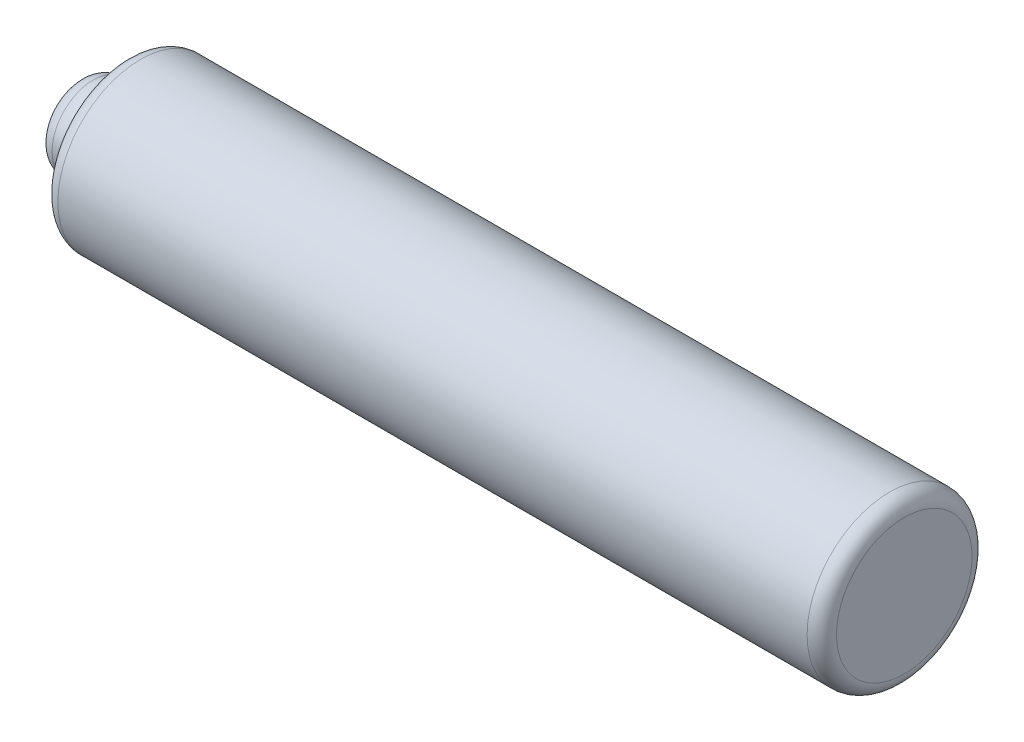
SolidWorks part; units mm, degrees
material "Copper"
ref_plane "Front Plane" through (0, 0, 0) normal (0, 0, 1) x (1, 0, 0)
ref_plane "Top Plane" through (0, 0, 0) normal (0, 1, 0) x (1, 0, 0)
ref_plane "Right Plane" through (0, 0, 0) normal (1, 0, 0) x (0, 0, -1)
sketch "Sketch1" plane through (0, 0, 0) normal (0, 1, 0) x (1, 0, 0)
  line L1 (-45.8444, 21.4949) -> (-5.4513, 21.4949)
  line L2 (-45.8444, 21.4949) -> (-45.8444, 19.355)
  line L3 (-45.8444, 17.2152) -> (-5.4513, 17.2152)
  line L4 (-5.4513, 21.4949) -> (-5.4513, 17.2152)
  line L5 (-45.8444, 19.355) -> (-48.2854, 19.355)
  line L7 (-45.8444, 17.2152) -> (-48.2854, 17.2152)
  line L8 (-48.2854, 19.355) -> (-48.2854, 17.2152)
revolve "Revolve1" add sketch "Sketch1" angle 360 about L3
fillet "Fillet2" radius 0.762 3 edges at (-48.2854, 0, -15.0754) (-45.8444, 0, -12.9355) (-5.4513, 0, -12.9355)
